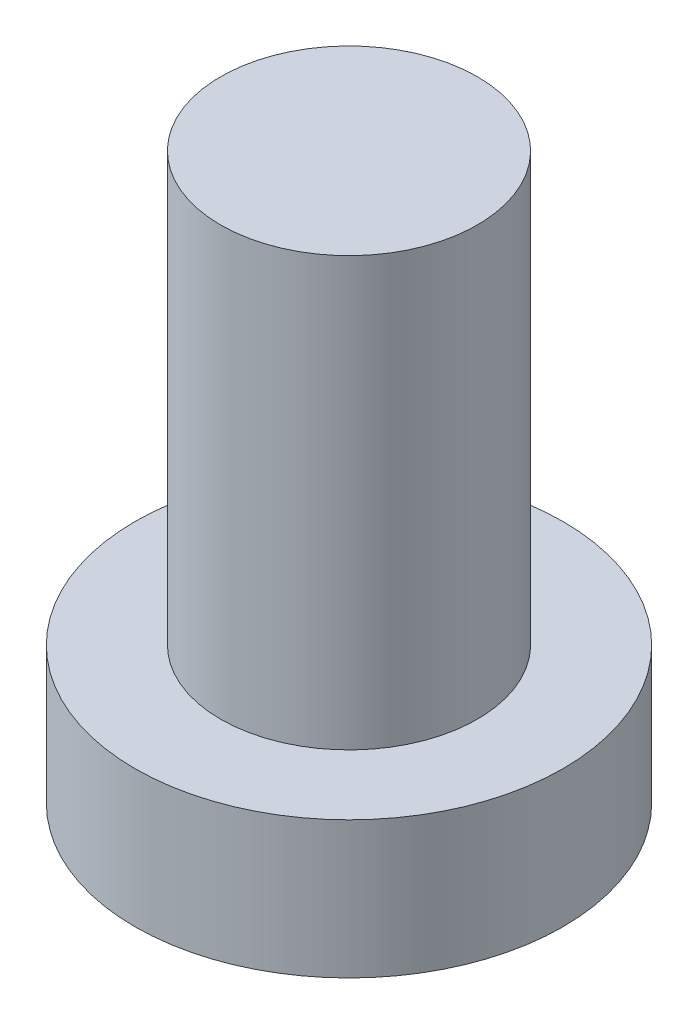
SolidWorks part; units mm, degrees
ref_plane "前视基准面" through (0, 0, 0) normal (0, 0, 1) x (1, 0, 0)
ref_plane "上视基准面" through (0, 0, 0) normal (0, 1, 0) x (1, 0, 0)
ref_plane "右视基准面" through (0, 0, 0) normal (1, 0, 0) x (0, 0, -1)
sketch "草图1" plane through (0, 0, 0) normal (0, 1, 0) x (1, 0, 0)
  circle A0 centre (0, 0) radius 2.5
extrude "凸台-拉伸1" add sketch "草图1" along normal blind 1.6
sketch "草图2" plane through (0, 1.6, 0) normal (0, 1, 0) x (1, 0, 0)
  circle A0 centre (0, 0) radius 1.5
extrude "凸台-拉伸2" add sketch "草图2" along normal blind 5
sketch "草图3" plane through (0, 0, 0) normal (0, -1, 0) x (1, 0, 0)
  line L0 (-0.5, 1) -> (-0.5, 1.75)
  line L1 (-1.75, -0.5) -> (-1, -0.5)
  line L2 (-1.75, -0.5) -> (-1.75, 0.5)
  line L3 (-1.75, 0.5) -> (-1, 0.5)
  line L4 (1.75, -0.5) -> (1.75, 0.5)
  line L5 (-1.75, -0.5) -> (1.75, 0.5) construction
  line L6 (-1.75, 0.5) -> (1.75, -0.5) construction
  line L7 (-0.5, -1.75) -> (0.5, -1.75)
  line L8 (-0.5, -1.75) -> (-0.5, -1)
  line L9 (-0.5, 1.75) -> (0.5, 1.75)
  line L10 (0.5, -1.75) -> (0.5, -1)
  line L11 (-0.5, -1.75) -> (0.5, 1.75) construction
  line L12 (-0.5, 1.75) -> (0.5, -1.75) construction
  line L13 (1, -0.5) -> (1.75, -0.5)
  line L14 (0.5, 1) -> (0.5, 1.75)
  line L15 (1, 0.5) -> (1.75, 0.5)
  arc A0 (1, -0.5) -> (0.5, -1) centre (1, -1) ccw
  arc A1 (-0.5, -1) -> (-1, -0.5) centre (-1, -1) ccw
  arc A2 (0.5, 1) -> (1, 0.5) centre (1, 1) ccw
  arc A3 (-0.5, 1) -> (-1, 0.5) centre (-1, 1) cw
  point P0 (0, 0)
  point P6 (0, 0)
  point P21 (0.5, 0.5)
  dimension "D1" = 0.5
extrude "切除-拉伸1" cut sketch "草图3" against normal blind 1
